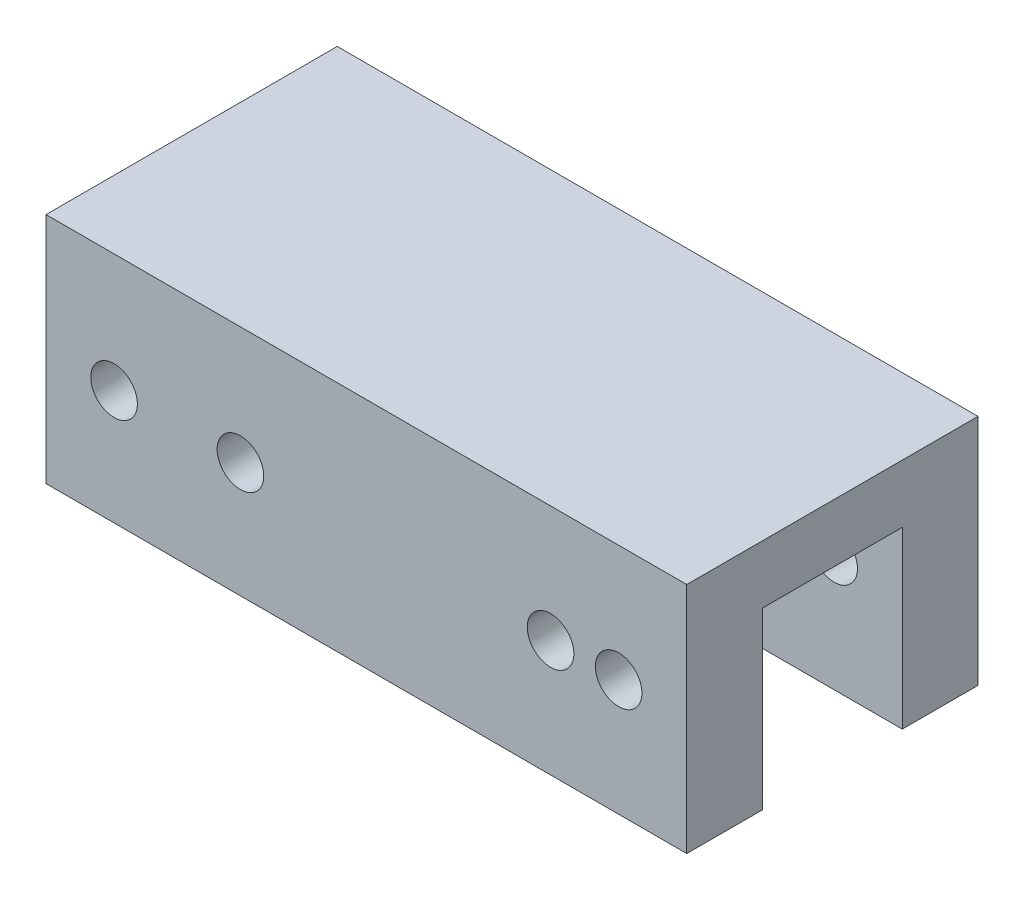
SolidWorks part; units mm, degrees
ref_plane "Alzado" through (0, 0, 0) normal (0, 0, 1) x (1, 0, 0)
ref_plane "Planta" through (0, 0, 0) normal (0, 1, 0) x (1, 0, 0)
ref_plane "Vista lateral" through (0, 0, 0) normal (1, 0, 0) x (0, 0, -1)
sketch "Croquis4" plane through (0, 0, 0) normal (0, 1, 0) x (1, 0, 0)
  line L1 (30.2258, -8.5161) -> (-24.7742, -8.5161)
  line L2 (30.2258, -8.5161) -> (30.2258, 16.4839)
  line L3 (30.2258, 16.4839) -> (-24.7742, 16.4839)
  line L4 (-24.7742, -8.5161) -> (-24.7742, 16.4839)
  dimension "D1" = 25
  dimension "D2" = 55
extrude "Saliente-Extruir3" add sketch "Croquis4" along normal blind 20
sketch "Croquis5" plane through (0, 0, 0) normal (0, -1, 0) x (-1, 0, 0)
  line L0 (24.7742, -8.5161) -> (24.7742, -2.0161) construction
  line L2 (24.7742, 16.4839) -> (24.7742, -8.5161) construction
  line L3 (24.7742, 16.4839) -> (24.7742, 9.9839) construction
  line L4 (24.7742, -2.0161) -> (24.7742, 9.9839)
  line L5 (24.7742, 9.9839) -> (-30.2258, 9.9839)
  line L6 (-30.2258, -8.5161) -> (-30.2258, 16.4839) construction
  line L7 (-30.2258, 9.9839) -> (-30.2258, -2.0161)
  line L8 (-30.2258, -2.0161) -> (24.7742, -2.0161)
  dimension "D1" = 6.5
  dimension "D2" = 6.5
extrude "Cortar-Extruir1" cut sketch "Croquis5" against normal blind 15
sketch "Croquis6" plane through (0, 0, -16.4839) normal (0, 0, -1) x (-1, 0, 0)
  line L0 (-30.2258, 10) -> (-18.5358, 10) construction
  line L2 (-18.5358, 10) -> (-18.5358, 21.0983) construction
  line L3 (-18.5358, 21.0983) -> (-18.5358, -1.5893) construction
  line L4 (-30.2258, 20) -> (-30.2258, 0) construction
  line L5 (-30.2258, 10) -> (-24.3808, 10)
  point P1 (-24.3808, 10)
  dimension "D1" = 5.845
sketch "Croquis7" plane through (0, 0, -16.4839) normal (0, 0, -1) x (-1, 0, 0)
  circle A0 centre (-24.3808, 10) radius 2
  circle A1 centre (-18.5358, 10) radius 2
  dimension "D1" = 4
extrude "Cortar-Extruir3" cut sketch "Croquis7" against normal through all both and the other way through all
sketch "Croquis8" plane through (0, 0, -16.4839) normal (0, 0, -1) x (-1, 0, 0)
  line L0 (-2.7258, 20) -> (-2.7258, -2.1023) construction
  line L1 (-30.2258, 20) -> (24.7742, 20) construction
sketch "Croquis10" plane through (0, 0, 2.0161) normal (0, 0, -1) x (-1, 0, 0)
  line L0 (-18.5358, 10) -> (28.7045, 10) construction
sketch "Croquis12" plane through (0, 0, -16.4839) normal (0, 0, -1) x (-1, 0, 0)
  line L0 (24.7742, 20) -> (24.7742, 0) construction
  point P0 (18.9292, 9.8388)
  dimension "D1" = 5.845
sketch "Croquis13" plane through (0, 0, -16.4839) normal (0, 0, -1) x (-1, 0, 0)
  line L0 (-2.7258, 20) -> (-2.7258, -2.1023) construction
  point P0 (8.0842, 9.9036)
  dimension "D1" = 10.81
sketch "Croquis14" plane through (0, 0, -16.4839) normal (0, 0, -1) x (-1, 0, 0)
  circle A0 centre (8.0842, 9.9036) radius 2
  circle A1 centre (18.9292, 9.8388) radius 2
  dimension "D1" = 4
extrude "Cortar-Extruir6" cut sketch "Croquis14" against normal blind 35
